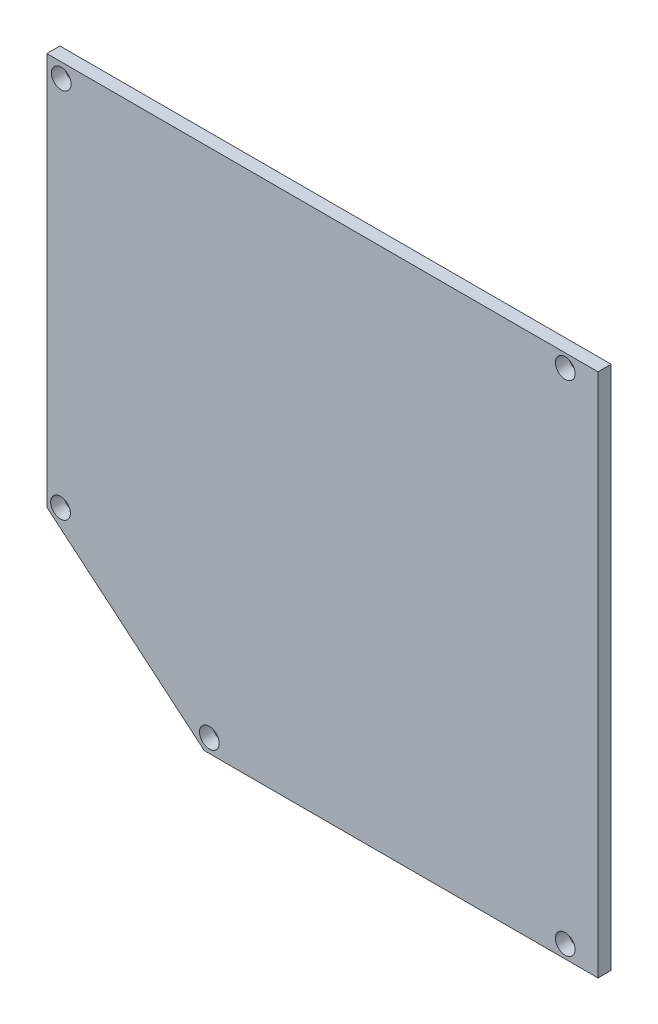
SolidWorks part; units mm, degrees
ref_plane "Front Plane" through (0, 0, 0) normal (0, 0, 1) x (1, 0, 0)
ref_plane "Top Plane" through (0, 0, 0) normal (0, 1, 0) x (1, 0, 0)
ref_plane "Right Plane" through (0, 0, 0) normal (1, 0, 0) x (0, 0, -1)
sketch "Croquis1" plane through (0, 0, 0) normal (0, 0, 1) x (1, 0, 0)
  line L0 (0, 0) -> (60, 0)
  line L2 (0, 0) -> (-24, 20.1384)
  line L9 (60, 80) -> (60, 0)
  line L14 (-24, 20.1384) -> (-24, 80)
  line L19 (-24, 80) -> (60, 80)
extrude "Saliente-Extruir1" add sketch "Croquis1" along normal blind 2
sketch "Croquis9" plane through (0, 0, 2) normal (0, 0, 1) x (1, 0, 0)
  line L0 (-20, 76) -> (-24, 80) construction
  line L1 (-20, 22.0036) -> (-24, 20.1384) construction
  line L2 (1.4559, 4) -> (0, 0) construction
  line L3 (55, 0) -> (55, 4) construction
  line L4 (0, 0) -> (60, 0) construction
  line L6 (55, 80) -> (55, 76) construction
  line L7 (60, 80) -> (-24, 80) construction
  line L38 (60, 80) -> (60, 0) construction
  line L43 (56, 4) -> (56, 76)
  line L44 (56, 76) -> (-20, 76)
  line L45 (-20, 76) -> (-20, 22.0036)
  line L46 (1.4559, 4) -> (56, 4)
  line L47 (-20, 22.0036) -> (1.4559, 4)
  line L48 (56, 4) -> (56, 76) construction
  line L49 (56, 76) -> (-20, 76) construction
  line L50 (-20, 76) -> (-20, 22.0036) construction
  line L51 (1.4559, 4) -> (56, 4) construction
  line L52 (-20, 22.0036) -> (1.4559, 4) construction
  circle A0 centre (-21.808, 77.808) radius 1.5
  circle A1 centre (-21.9155, 21.1104) radius 1.5
  circle A2 centre (0.7643, 2.1) radius 1.5
  circle A3 centre (55, 78) radius 1.5
  circle A4 centre (55, 2) radius 1.5
extrude "Cortar-Extruir5" cut sketch "Croquis9" against normal blind 6
equation "\"ancho\"= 84mm"
equation "\"lateral\"= 80mm"
equation "\"angulo\"= 40°"
equation "\"anchomenor\"= 60mm"
equation "\"D3@Croquis1\"=\"ancho\""
equation "\"D2@Croquis1\"=\"lateral\""
equation "\"D1@Croquis1\"=\"anchomenor\""
equation "\"D4@Croquis1\"=\"angulo\""
equation "\"r3\"= 3mm"
equation "\"D3@Croquis9\"=\"r3\""
